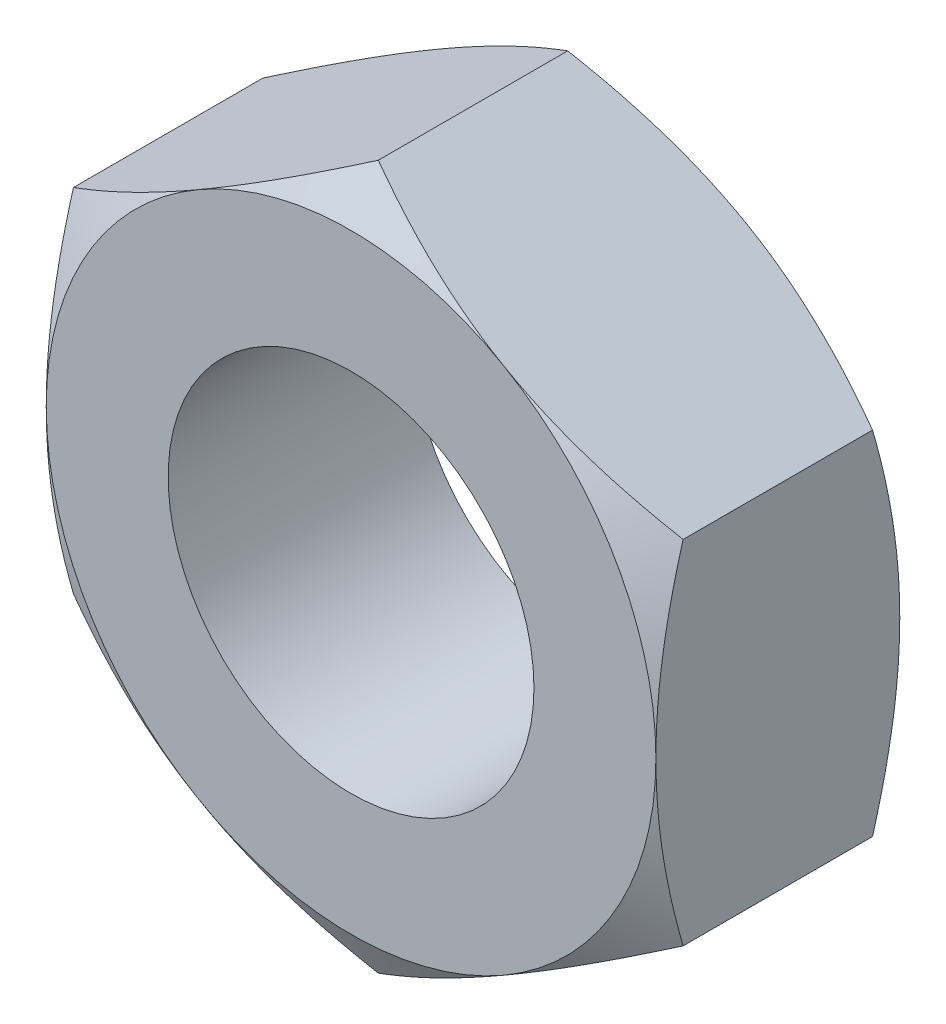
SolidWorks part; units mm, degrees
material "AISI 1045 Acero estirado en frío"
ref_plane "Front Plane" through (0, 0, 0) normal (0, 0, 1) x (1, 0, 0)
ref_plane "Top Plane" through (0, 0, 0) normal (0, 1, 0) x (1, 0, 0)
ref_plane "Right Plane" through (0, 0, 0) normal (1, 0, 0) x (0, 0, -1)
sketch "Sketch1" plane through (0, 0, 0) normal (0, 0, 1) x (1, 0, 0)
  line L1 (0, -2.8868) -> (2.5, -1.4434)
  line L2 (2.5, -1.4434) -> (2.5, 1.4434)
  line L3 (2.5, 1.4434) -> (0, 2.8868)
  line L4 (0, 2.8868) -> (-2.5, 1.4434)
  line L5 (-2.5, 1.4434) -> (-2.5, -1.4434)
  line L6 (-2.5, -1.4434) -> (0, -2.8868)
  circle A0 centre (0, 0) radius 1.5
  circle A1 centre (0, 0) radius 2.5 construction
  dimension "D1" = 5
  dimension "D2" = 3
extrude "Boss-Extrude1" add sketch "Sketch1" along normal blind 2
cosmetic thread "Cosmetic Thread1" parameters "D2"=4
sketch "Sketch2" plane through (0, 0, 2) normal (0, 0, 1) x (1, 0, 0)
  circle A0 centre (0, 0) radius 2.5 construction
  circle A1 centre (0, 0) radius 2.5
extrude "Cut-Extrude1" cut sketch "Sketch2" against normal blind 2 draft 60 flip side to cut
sketch "Sketch3" plane through (0, 0, 0) normal (0, 0, -1) x (-1, 0, 0)
  circle A0 centre (0, 0) radius 2.5 construction
  circle A1 centre (0, 0) radius 2.5
extrude "Cut-Extrude2" cut sketch "Sketch3" against normal blind 2 draft 60 flip side to cut
